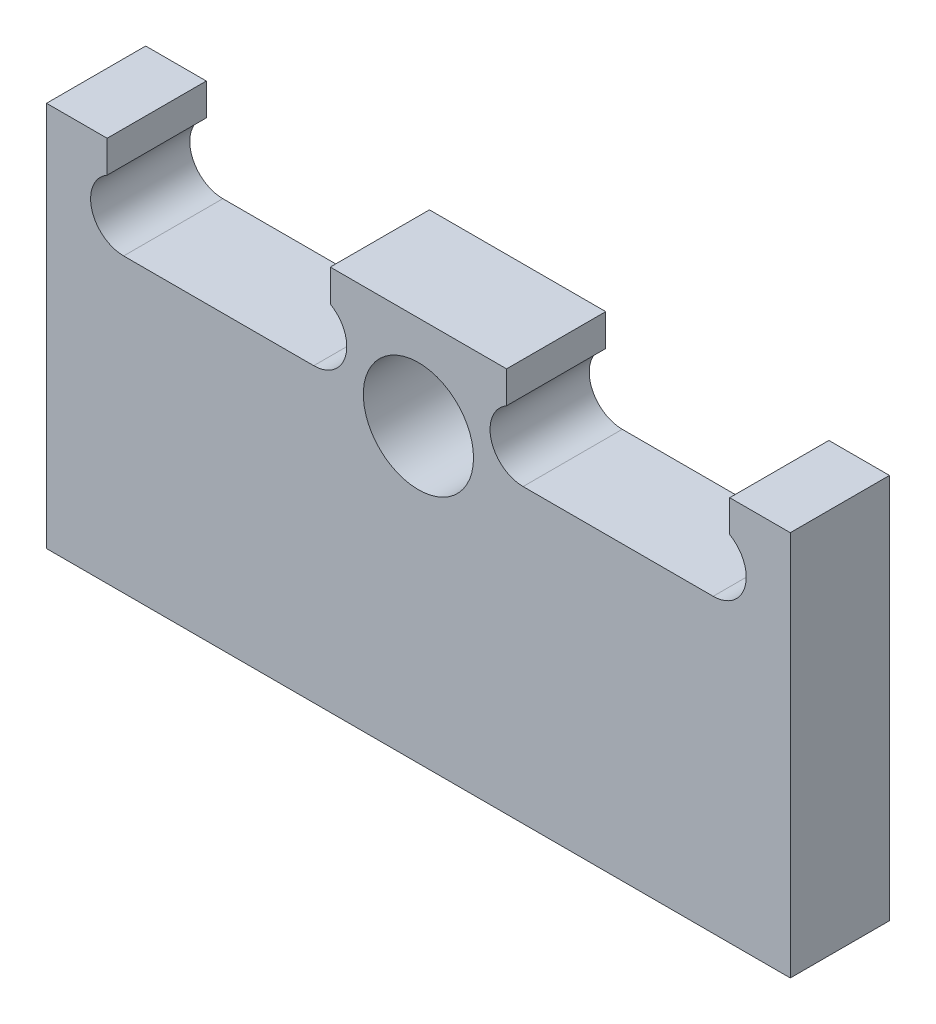
SolidWorks part; units mm, degrees
ref_plane "Alzado" through (0, 0, 0) normal (0, 0, 1) x (1, 0, 0)
ref_plane "Planta" through (0, 0, 0) normal (0, 1, 0) x (1, 0, 0)
ref_plane "Vista lateral" through (0, 0, 0) normal (1, 0, 0) x (0, 0, -1)
sketch "Croquis1" plane through (0, 0, 0) normal (0, 0, 1) x (1, 0, 0)
  line L0 (0, 0) -> (0, 70)
  line L1 (0, 70) -> (11, 70)
  line L2 (135, 70) -> (135, 0)
  line L3 (135, 0) -> (0, 0)
  line L4 (0, 59) -> (14, 59) construction
  line L5 (14, 59) -> (14, 70) construction
  line L6 (48.5, 53) -> (14, 53)
  line L7 (67.5, 0) -> (67.5, 70) construction
  line L8 (11, 70) -> (11, 64.1962)
  line L9 (51.5, 70) -> (51.5, 64.1962)
  line L10 (51.5, 70) -> (83.5, 70)
  line L11 (124, 70) -> (124, 64.1962)
  line L12 (83.5, 70) -> (83.5, 64.1962)
  line L13 (86.5, 53) -> (121, 53)
  line L14 (124, 70) -> (135, 70)
  arc A0 (11, 64.1962) -> (14, 53) centre (14, 59) ccw
  arc A1 (48.5, 53) -> (51.5, 64.1962) centre (48.5, 59) ccw
  arc A2 (86.5, 53) -> (83.5, 64.1962) centre (86.5, 59) cw
  arc A3 (124, 64.1962) -> (121, 53) centre (121, 59) cw
  circle A4 centre (67.5, 53) radius 10
  dimension "D5" = 34.5
  dimension "D9" = 17
  dimension "D1" = 70
  dimension "D2" = 135
  dimension "D3" = 14
  dimension "D4" = 11
  dimension "D6" = 11
  dimension "D7" = 40.5
  dimension "D8" = 70
extrude "Saliente-Extruir1" add sketch "Croquis1" along normal blind 18
